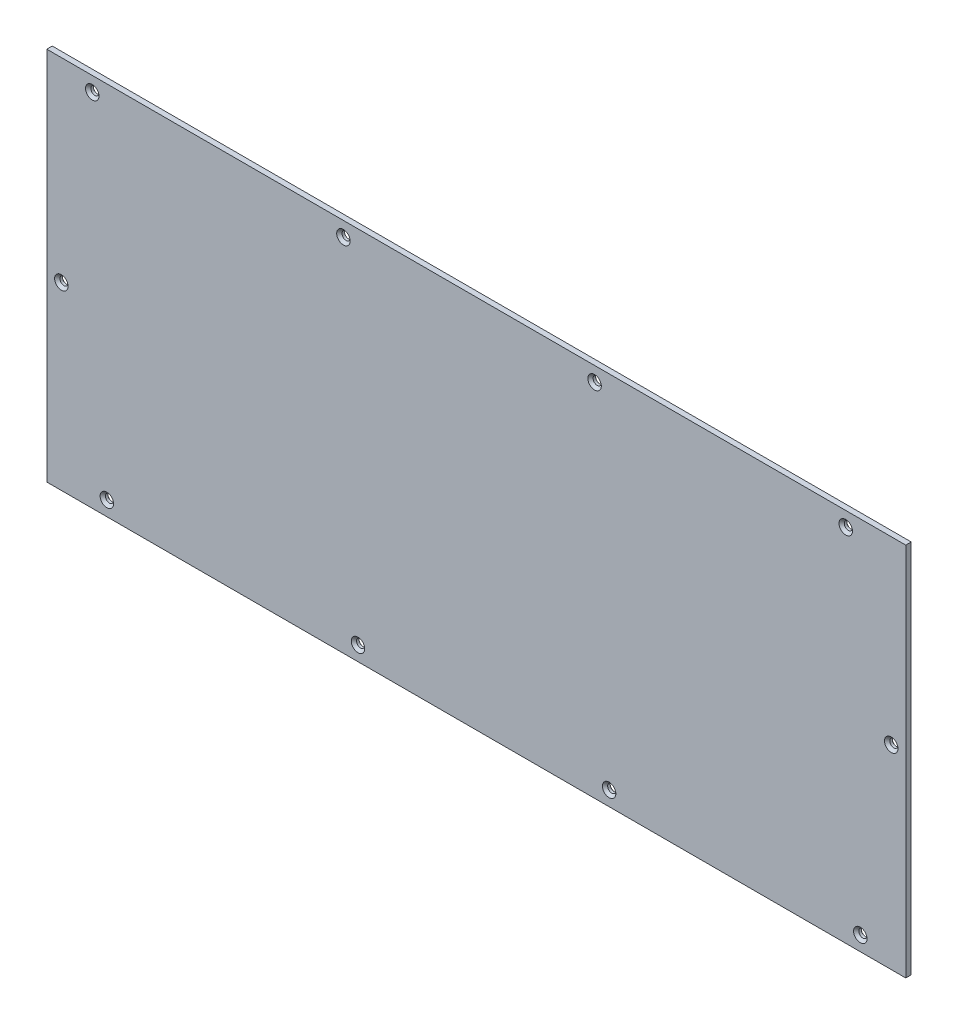
SolidWorks part; units mm, degrees
ref_plane "Спереди" through (0, 0, 0) normal (0, 0, 1) x (1, 0, 0)
ref_plane "Сверху" through (0, 0, 0) normal (0, 1, 0) x (1, 0, 0)
ref_plane "Справа" through (0, 0, 0) normal (1, 0, 0) x (0, 0, -1)
sketch "Эскиз1" plane through (0, 0, 0) normal (0, 0, 1) x (1, 0, 0)
  line L1 (0, 0) -> (472, 0)
  line L2 (0, 0) -> (0, 206)
  line L3 (0, 206) -> (472, 206)
  line L4 (472, 0) -> (472, 206)
  dimension "D1" = 472
  dimension "D2" = 206
extrude "Бобышка-Вытянуть1" add sketch "Эскиз1" along normal blind 3
hole_wizard "Зенковка для винта с потайной головкой M41" positions "Эскиз3" profile "Эскиз2" countersink size "M4" standard "DIN" end condition through all
sketch "Эскиз3" plane through (0, 0, 3) normal (0, 0, 1) x (1, 0, 0)
  line L0 (0, 206) -> (0, 0) construction
  line L1 (472, 206) -> (0, 206) construction
  line L3 (472, 0) -> (472, 206) construction
  line L4 (0, 0) -> (472, 0) construction
  point P0 (25, 198)
  point P1 (163, 198)
  point P3 (301, 198)
  point P5 (439, 198)
  point P7 (447, 8)
  point P9 (309, 8)
  point P11 (171, 8)
  point P13 (33, 8)
  point P15 (8, 99)
  point P17 (464, 107)
  dimension "D1" = 138
  dimension "D2" = 138
  dimension "D3" = 138
  dimension "D4" = 25
  dimension "D5" = 8
  dimension "D6" = 25
  dimension "D7" = 8
  dimension "D8" = 99
  dimension "D9" = 456
  dimension "D10" = 138
  dimension "D11" = 138
  dimension "D12" = 138
  dimension "D13" = 190
  dimension "D14" = 99
sketch "Эскиз2" plane through (25, 198, 3) normal (1, 0, 0) x (0, -1, 0)
  line L0 (0, 0) -> (0, 3)
  line L1 (0, 3) -> (2.4, 3)
  line L2 (2.25, 2.85) -> (2.25, 1.45)
  line L3 (2.25, 1.45) -> (3.7, 0)
  line L5 (3.7, 0) -> (0, 0)
  line L6 (-2.25, 1.45) -> (-3.7, 0) construction
  line L7 (2.4, 3) -> (2.25, 2.85)
  line L8 (-2.4, 3) -> (-2.25, 2.85) construction
  line L11 (0, -6.35) -> (0, 107.95) construction
  dimension "Диаметр сквозного отверстия" = 4.5
  dimension "Глубина сквозного отверстия" = 3
  dimension "Диаметр передней зенковки" = 7.4
  dimension "Угол передней зенковки" = 90
  dimension "Диаметр задней зенковки" = 4.8
  dimension "Угол задней зенковки" = 90
